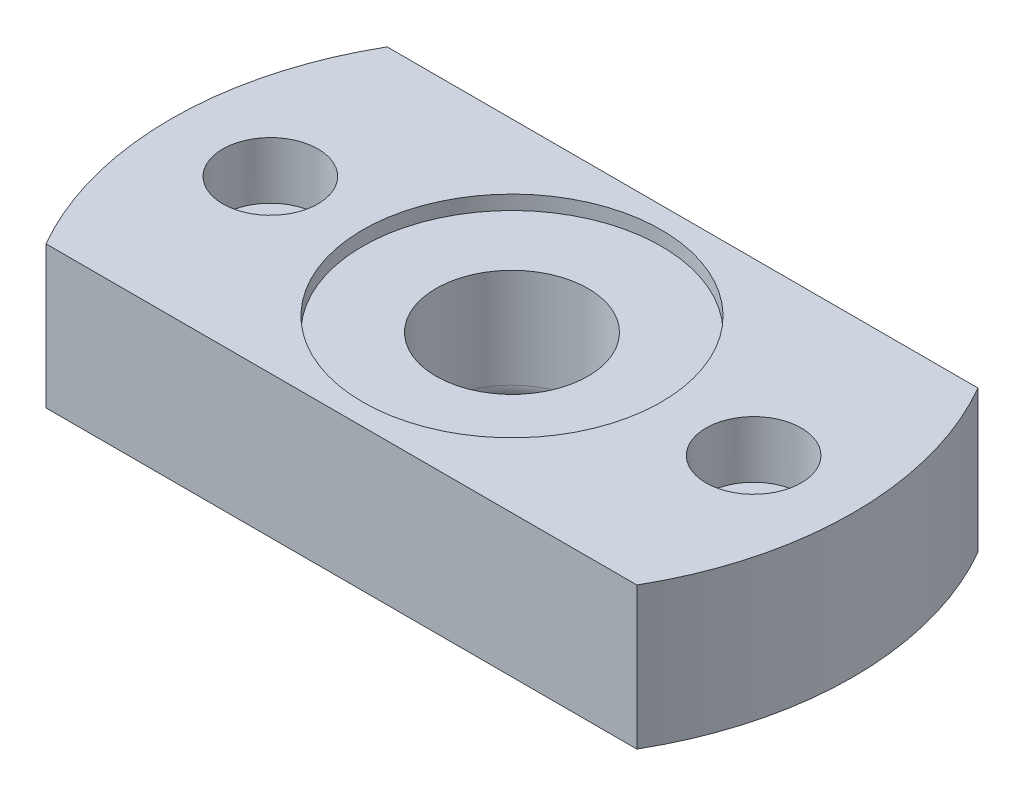
SolidWorks part; units mm, degrees
ref_plane "Front Plane" through (0, 0, 0) normal (0, 0, 1) x (1, 0, 0)
ref_plane "Top Plane" through (0, 0, 0) normal (0, 1, 0) x (1, 0, 0)
ref_plane "Right Plane" through (0, 0, 0) normal (1, 0, 0) x (0, 0, -1)
sketch "Sketch1" plane through (0, 0, 0) normal (0, 1, 0) x (1, 0, 0)
  circle A0 centre (0, 0) radius 12
  circle A1 centre (0, 0) radius 2.675
  dimension "D1" = 24
  dimension "D2" = 5.35
extrude "Boss-Extrude1" add sketch "Sketch1" along normal blind 5
sketch "Sketch3" plane through (0, 5, 0) normal (0, 1, 0) x (1, 0, 0)
  line L0 (-8.5, 0) -> (8.5, 0) construction
  circle A2 centre (-8.5, 0) radius 1.675
  circle A3 centre (8.5, 0) radius 1.675
  dimension "D1" = 3.35
  dimension "D2" = 17
  dimension "D3" = 8.5
extrude "Cut-Extrude1" cut sketch "Sketch3" against normal blind 6
sketch "Sketch4" plane through (0, 0, 0) normal (0, -1, 0) x (1, 0, 0)
  line L0 (0, 0) -> (0, 12) construction
  line L1 (-11.425, -1.6887) -> (-8.5, -3.3775)
  line L2 (-8.5, -3.3775) -> (-5.575, -1.6887)
  line L3 (-5.575, -1.6887) -> (-5.575, 1.6887)
  line L4 (-5.575, 1.6887) -> (-8.5, 3.3775)
  line L5 (-8.5, 3.3775) -> (-11.425, 1.6887)
  line L6 (-11.425, 1.6887) -> (-11.425, -1.6887)
  line L7 (11.425, 1.6887) -> (11.425, -1.6887)
  line L8 (8.5, 3.3775) -> (11.425, 1.6887)
  line L9 (5.575, 1.6887) -> (8.5, 3.3775)
  line L10 (5.575, -1.6887) -> (5.575, 1.6887)
  line L11 (8.5, -3.3775) -> (5.575, -1.6887)
  line L12 (11.425, -1.6887) -> (8.5, -3.3775)
  circle A0 centre (-8.5, 0) radius 2.925 construction
  circle A1 centre (0, 0) radius 12 construction
  circle A2 centre (8.5, 0) radius 2.925 construction
  dimension "D1" = 5.85
extrude "Cut-Extrude2" cut sketch "Sketch4" against normal blind 2.5
sketch "Sketch6" plane through (0, 0, 0) normal (0, -1, 0) x (1, 0, 0)
  line L0 (-12, 0) -> (12, 0) construction
  line L1 (-10.3923, 6) -> (10.3923, 6)
  line L2 (-10.3923, -6) -> (10.3923, -6)
  line L4 (-12, 6) -> (12, 6) construction
  line L5 (-12, -6) -> (12, -6) construction
  circle A0 centre (0, 0) radius 12 construction
  arc A1 (-10.3923, -6) -> (10.3923, -6) centre (0, 0) ccw
  arc A2 (10.3923, 6) -> (-10.3923, 6) centre (0, 0) ccw
  dimension "D1" = 6
  dimension "D2" = 6
extrude "Cut-Extrude4" cut sketch "Sketch6" against normal blind 10
fillet "Fillet1" radius 1 1 edges at (0, 0, 2.675)
sketch "Sketch7" plane through (0, 5, 0) normal (0, 1, 0) x (1, 0, 0)
  circle A0 centre (0, 0) radius 5.25
  dimension "D1" = 10.5
extrude "Cut-Extrude5" cut sketch "Sketch7" against normal blind 0.5
sketch "Sketch8" plane through (0, 2.5, 0) normal (0, -1, 0) x (1, 0, 0)
  circle A0 centre (8.5, 0) radius 1.675
  circle A1 centre (-8.5, 0) radius 1.675
extrude "Boss-Extrude2" add sketch "Sketch8" against normal blind 0.5
